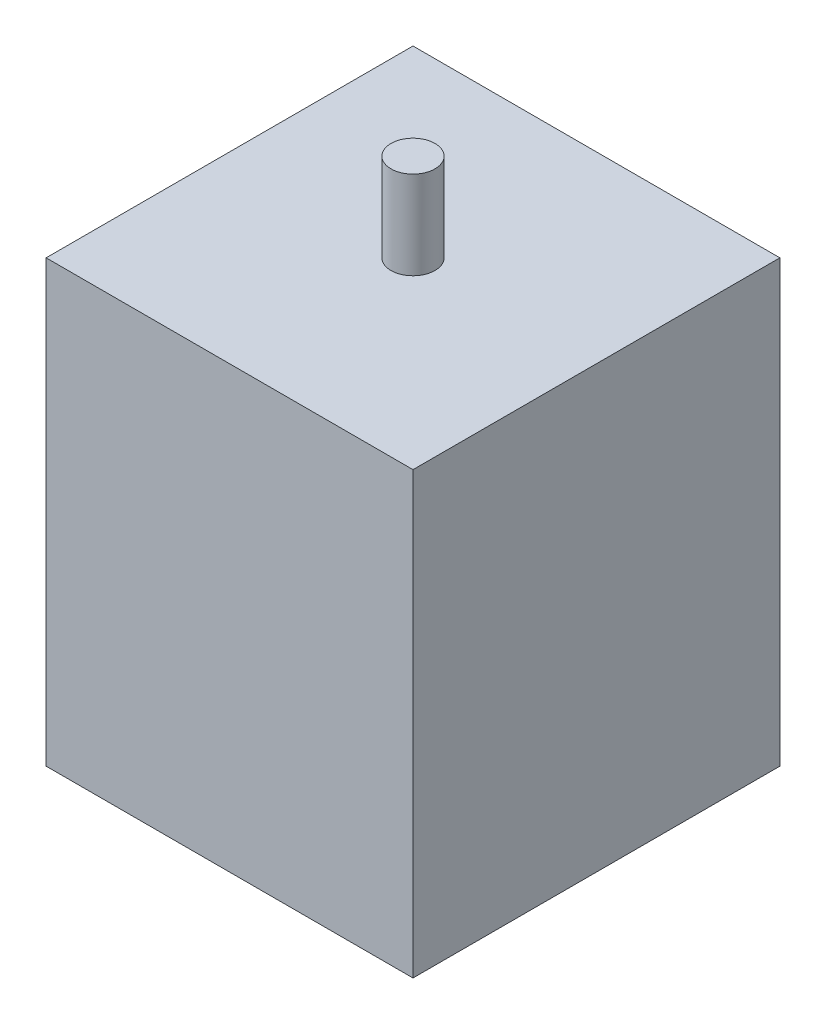
SolidWorks part; units mm, degrees
ref_plane "Front Plane" through (0, 0, 0) normal (0, 0, 1) x (1, 0, 0)
ref_plane "Top Plane" through (0, 0, 0) normal (0, 1, 0) x (1, 0, 0)
ref_plane "Right Plane" through (0, 0, 0) normal (1, 0, 0) x (0, 0, -1)
sketch "Sketch1" plane through (0, 0, 0) normal (0, 1, 0) x (1, 0, 0)
  line L1 (-25, -25) -> (25, -25)
  line L2 (-25, -25) -> (-25, 25)
  line L3 (-25, 25) -> (25, 25)
  line L4 (25, -25) -> (25, 25)
  line L5 (-25, -25) -> (25, 25) construction
  line L6 (-25, 25) -> (25, -25) construction
  point P0 (0, 0)
extrude "Boss-Extrude1" add sketch "Sketch1" along normal blind 60
sketch "Sketch2" plane through (0, 60, 0) normal (0, 1, 0) x (1, 0, 0)
  circle A0 centre (0, 0) radius 3
extrude "Boss-Extrude2" add sketch "Sketch2" along normal blind 12
